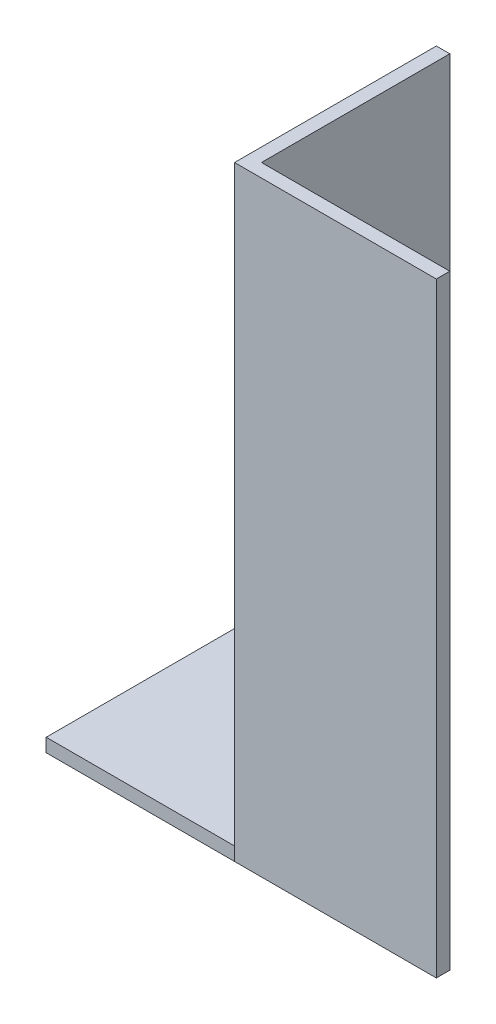
SolidWorks part; units mm, degrees
material "1060 Сплав"
ref_plane "Спереди" through (0, 0, 0) normal (0, 0, 1) x (1, 0, 0)
ref_plane "Сверху" through (0, 0, 0) normal (0, 1, 0) x (1, 0, 0)
ref_plane "Справа" through (0, 0, 0) normal (1, 0, 0) x (0, 0, -1)
sketch "Эскиз1" plane through (0, 0, 0) normal (0, 1, 0) x (1, 0, 0)
  line L0 (0, 0) -> (0, 15)
  line L1 (0, 15) -> (1, 15)
  line L2 (1, 15) -> (1, 1)
  line L3 (1, 1) -> (15, 1)
  line L4 (15, 1) -> (15, 0)
  line L5 (15, 0) -> (0, 0)
  dimension "D1" = 1
  dimension "D2" = 15
extrude "Бобышка-Вытянуть1" add sketch "Эскиз1" along normal blind 65
sketch "Эскиз2" plane through (0, 0, 0) normal (-1, 0, 0) x (0, 0, 1)
  point P0 (0, 0)
sketch "Эскиз3" plane through (0, 0, 0) normal (0, -1, 0) x (1, 0, 0)
  line L0 (1, -1) -> (0, -1)
  line L6 (15, 0) -> (0, 0)
  line L7 (0, 0) -> (0, -15)
  line L8 (0, -15) -> (1, -15)
  line L9 (1, -15) -> (1, -1)
  line L10 (1, -1) -> (15, -1)
  line L11 (15, -1) -> (15, 0)
  line L13 (0, -1) -> (0, -15)
  line L14 (0, -15) -> (1, -15)
  line L15 (1, -15) -> (1, -1)
  dimension "D1" = 0
extrude "Вырез-Вытянуть1" cut sketch "Эскиз3" against normal blind 20
sketch "Эскиз5" plane through (1, 0, 0) normal (1, 0, 0) x (0, 0, -1)
  line L1 (15, 20) -> (1, 20)
  line L2 (15, 20) -> (15, 19)
  line L3 (1, 20) -> (1, 19)
  line L4 (15, 19) -> (1, 19)
  dimension "D1" = 1
extrude "Бобышка-Вытянуть4" add sketch "Эскиз5" against normal blind 16
sketch "Эскиз6" plane through (0, 0, 0) normal (0, -1, 0) x (1, 0, 0)
  line L4 (0, 0) -> (0, -1)
  line L5 (0, -1) -> (15, -1)
  line L6 (15, -1) -> (15, 0)
  line L7 (15, 0) -> (0, 0)
  line L8 (0, 0) -> (0, -1)
  line L9 (0, -1) -> (15, -1)
  line L10 (15, -1) -> (15, 0)
  line L11 (15, 0) -> (0, 0)
  dimension "D1" = 0
extrude "Вырез-Вытянуть2" cut sketch "Эскиз6" against normal up to surface (19 mm away) up to face at (-5.6, 19, -6.6)
sketch "Эскиз7" plane through (0, 19, 0) normal (0, -1, 0) x (1, 0, 0)
  line L0 (15, 0) -> (15, -1)
  line L1 (15, 0) -> (0, 0)
  line L2 (15, -1) -> (0, -1)
  line L3 (0, 0) -> (0, -1)
  line L4 (0, -1) -> (0, 0) construction
extrude "Вырез-Вытянуть3" cut sketch "Эскиз7" against normal blind 1
